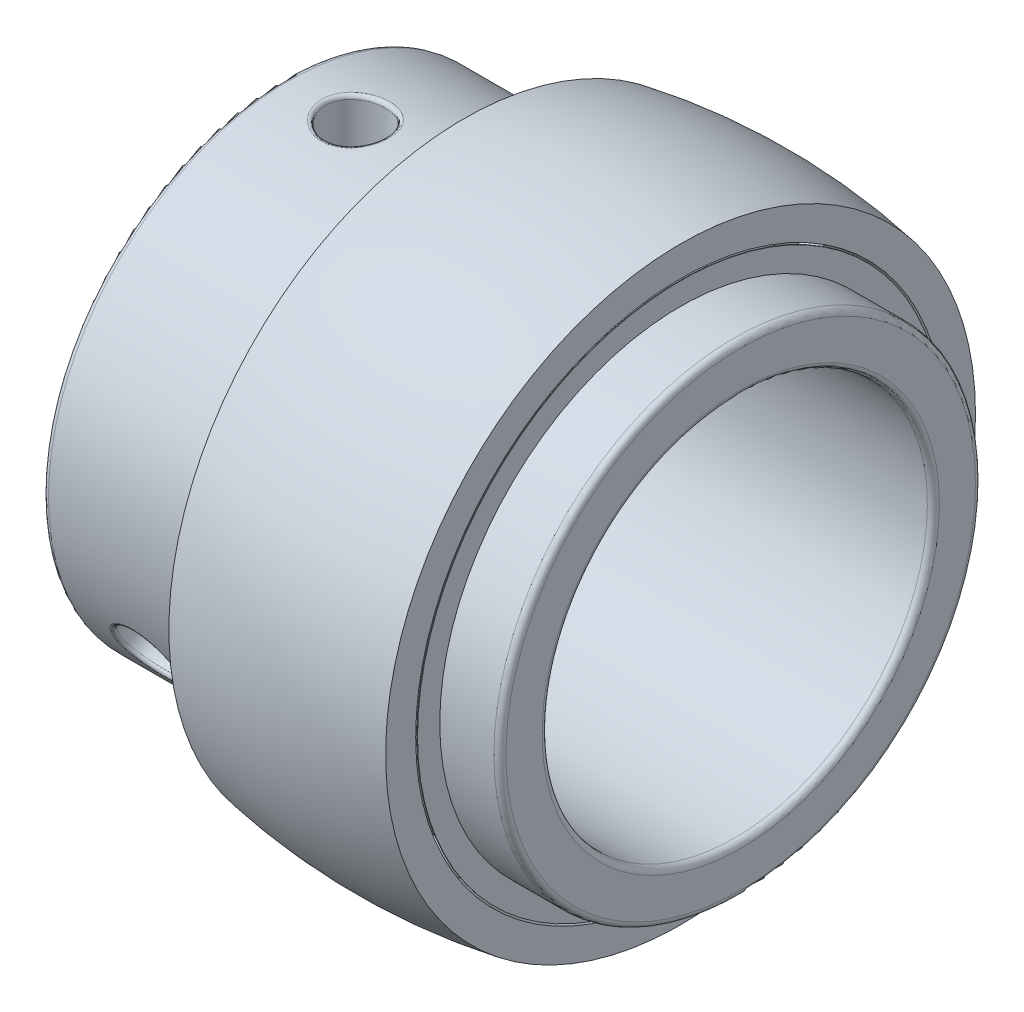
SolidWorks part; units mm, degrees
ref_plane "Ön Düzlem" through (0, 0, 0) normal (0, 0, 1) x (1, 0, 0)
ref_plane "Üst Düzlem" through (0, 0, 0) normal (0, 1, 0) x (1, 0, 0)
ref_plane "Sağ Düzlem" through (0, 0, 0) normal (1, 0, 0) x (0, 0, -1)
sketch "Çizim1" plane through (0, 0, 0) normal (0, 0, 1) x (1, 0, 0)
  line L0 (0, 0) -> (-8.6578, 0) construction
  line L1 (0, 0) -> (0, 23.25) construction
  line L2 (2.2913, 22) -> (9, 22)
  line L4 (-9, 24.5) -> (-9, 22)
  line L5 (-9, 22) -> (-2.2913, 22)
  line L6 (9, 24.5) -> (9, 22)
  line L7 (-9, 24.5) -> (9, 22) construction
  line L8 (-9, 22) -> (9, 24.5) construction
  line L9 (0, 23.25) -> (0, 30.6486) construction
  arc A0 (-9, 24.5) -> (9, 24.5) centre (0, -26.9183) cw
  arc A1 (2.2913, 22) -> (-2.2913, 22) centre (0, 21) ccw
  point P3 (0, 23.25)
  point P15 (0, 23.162)
  dimension "D3" = 52.2
  dimension "D5" = 5
  dimension "D1" = 2.5
  dimension "D2" = 18
  dimension "D4" = 24.5
  dimension "D6" = 21
revolve "Döndür1" add sketch "Çizim1" angle 360 about L0
sketch "Çizim2" plane through (0, 0, 0) normal (0, 0, 1) x (1, 0, 0)
  line L0 (0, -18.5) -> (0, -23.5)
  arc A0 (0, -23.5) -> (0, -18.5) centre (0, -21) ccw
  dimension "D1" = 5
  dimension "D2" = 21
revolve "Döndür2" add sketch "Çizim2" angle 360 about L0
pattern_circular "Dairesel Kaplama1" count 22 over 360 about axis through (0, 0, 0) along (1, 0, 0) of bodies 102
sketch "Çizim3" plane through (0, 0, 0) normal (0, 0, 1) x (1, 0, 0)
  line L0 (0, 32.0526) -> (0, 18.2497) construction
  line L1 (0, 0) -> (-30.1114, 0) construction
  line L2 (9, -24.5) -> (9, 24.5) construction
  line L3 (-24, 20) -> (-2.2913, 20)
  line L4 (-24, 20) -> (-24, 16)
  line L5 (-24, 16) -> (14, 16)
  line L6 (14, 20) -> (14, 16)
  line L7 (-9, 24.5) -> (-9, -24.5) construction
  line L8 (2.2913, 20) -> (14, 20)
  line L9 (0, 18.5) -> (0, 0) construction
  arc A0 (-2.2913, 20) -> (2.2913, 20) centre (0, 21) ccw
  point P17 (0, 18.5)
  point P18 (0, 18.2497)
  dimension "D5" = 5
  dimension "D6" = 21
  dimension "D1" = 4
  dimension "D2" = 5
  dimension "D3" = 15
  dimension "D4" = 16
  dimension "D7" = 16
revolve "Döndür3" add sketch "Çizim3" angle 360 about L1
sketch "Çizim4" plane through (-9, 0, 0) normal (-1, 0, 0) x (0, 0, 1)
  circle A0 centre (0, 0) radius 21.85
  circle A1 centre (0, 0) radius 20
  circle A2 centre (0, 0) radius 20
  dimension "D2" = 43.7
  dimension "D1" = 0
extrude "Yükseklik-Ekstrüzyon1" add sketch "Çizim4" against normal blind 0.05
mirror "Aynalama1" about plane through (0, 0, 0) normal (1, 0, 0) of "Yükseklik-Ekstrüzyon1"
fillet "Radyus1" radius 0.5 4 edges at (-24, 0, -16) (14, 0, -16) (14, 0, -20) (-24, 0, -20)
sketch "Çizim5" plane through (0, 0, 0) normal (0, 1, 0) x (1, 0, 0)
  circle A0 centre (-18, 0) radius 2.5
  point P2 (0, 0)
  dimension "D1" = 5
  dimension "D2" = 18
extrude "Kes-Ekstrüzyon1" cut sketch "Çizim5" along normal blind 39.05
pattern_circular "Dairesel Kaplama2" count 3 over 360 about axis through (-24, 0, 0) along (-1, 0, 0) of "Kes-Ekstrüzyon1"
fillet "Radyus2" radius 0.3 6 edges at (-18.5531, -7.814, -18.4104) (-17.459, -5.7926, -14.9146) (-18.5531, 19.8508, 2.438) (-17.459, 15.8127, 2.4408) (-18.5531, -12.0368, 15.9723) (-17.459, -10.0201, 12.4738)
